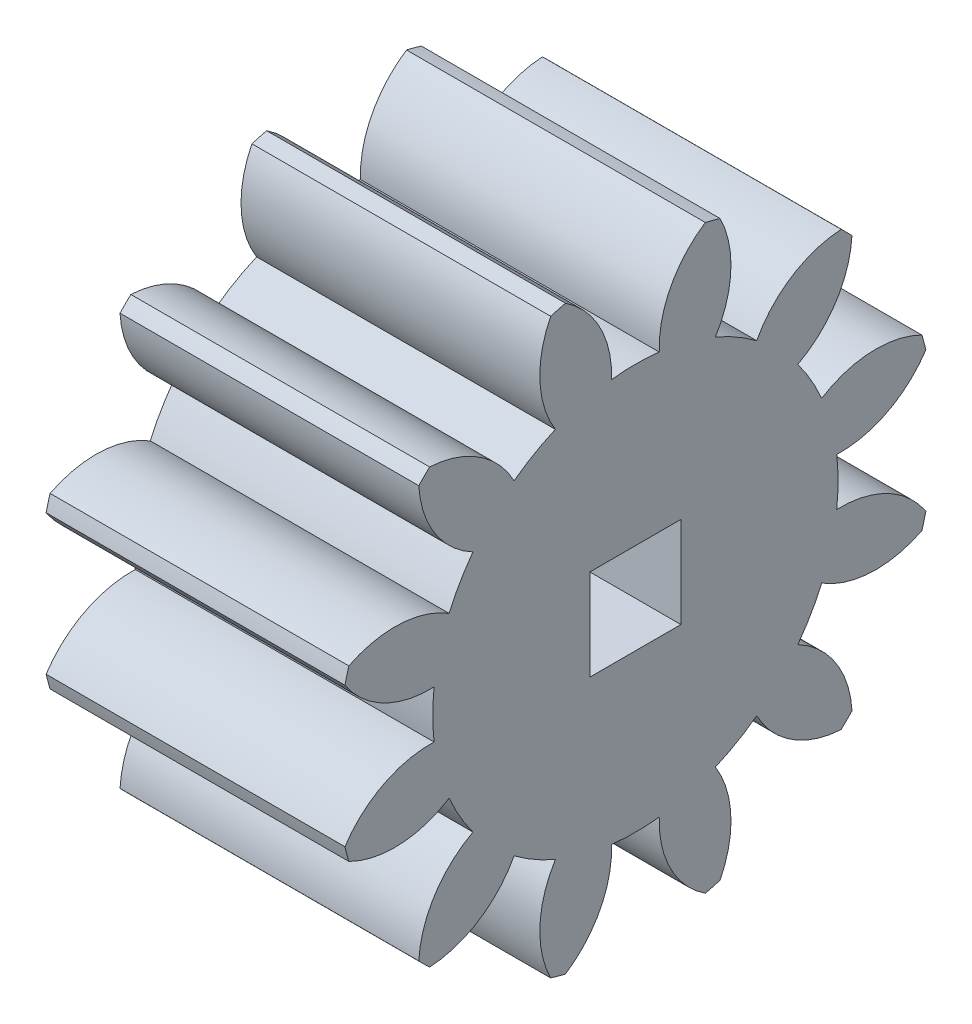
SolidWorks part; units mm, degrees
ref_plane "Plane1" through (0, 0, 0) normal (0, 0, 1) x (1, 0, 0)
ref_plane "Plane2" through (0, 0, 0) normal (0, 1, 0) x (1, 0, 0)
ref_plane "Plane3" through (0, 0, 0) normal (1, 0, 0) x (0, 0, -1)
other "Configuration Table"
sketch "HoldingSke" plane through (0, 0, 0) normal (0, 1, 0) x (1, 0, 0)
  line L0 (0, 0) -> (0.6521, -0.1386)
  line L1 (-15, 0) -> (100, 0) construction
  line L2 (0, 0) -> (-2.1039, 2.3779)
  line L3 (0, 0) -> (-11.863, 4.5341)
  line L4 (0, 0) -> (8.4473, 1.7955)
  line L5 (0, 0) -> (-46.8476, -17.4728)
  line L6 (0, 0) -> (-16.5793, -11.1861)
  line L7 (-2.1039, 2.3779) -> (8.6586, 51.2059)
  line L8 (-76.2, 54.61) -> (-76.1, 54.61)
  line L9 (-71.009, 38.7566) -> (-53.1078, 45.2721)
  line L10 (-76.2, 71.12) -> (104.1128, 71.12)
  line L11 (0, 0) -> (-20, 0)
  line L12 (-76.2, 101.6) -> (-76.147, 101.6)
  line L13 (24.9733, 27.94) -> (52.9518, 28.4284)
  line L14 (24.9733, 27.94) -> (24.9743, 27.94)
  line L15 (24.9733, 27.94) -> (100.4006, 29.5858)
  line L16 (-63.627, -1.5) -> (-12.827, -1.5)
  circle A0 centre (0, 0) radius 0.5
  circle A1 centre (0, 0) radius 7.124
  circle A2 centre (0, 0) radius 37.5
  circle A3 centre (0, 0) radius 0.5
  dimension "MHD" = 14.248
  dimension "Hub_dia" = 75
  dimension "Bore" = 1
  dimension "MBD" = 1
  dimension "Num_teeth" = 12
  dimension "Pitch" = 0.6667
  dimension "Overall_len" = 50
  dimension "Show_teeth" = 12
  dimension "Thickness" = 20
  dimension "OAL" = 50.0001
  dimension "T_dim" = 0.1
  dimension "Ap" = 20
  dimension "H" = 19.05
  dimension "Pitch_radius" = 180.3128
  dimension "Width" = 20
  dimension "Backlash" = 0.053
  dimension "Addendum_fac" = 1
  dimension "Dedendum_fac" = 1.25
  dimension "Clearance_fac" = 0.25
  dimension "Dedendum_add" = 0.001
  dimension "Module" = 1.5
sketch "BasProSke" plane through (0, 0, 0) normal (0, 1, 0) x (1, 0, 0)
  line L0 (-10, 0) -> (60, 0) construction
  line L1 (0, 0) -> (0, 10.5)
  line L2 (0, 0) -> (10.5, 0)
  line L3 (10.5, 0) -> (10.5, 10.5)
  line L4 (10.5, 10.5) -> (0, 10.5)
  dimension "Thickness" = 10.5
  dimension "Diameter" = 21
revolve "Base-Revolve" add sketch "BasProSke" angle 360 about L0
sketch "TooCutSke" plane through (0, 0, 0) normal (1, 0, 0) x (0, 0, -1)
  line L1 (0, 0) -> (0, 107) construction
  line L2 (0, 0) -> (-1.2674, 8.9103) construction
  line L3 (0, 0) -> (-4.625, 17.2606) construction
  line L4 (-1.2674, 8.9103) -> (-2.3125, 8.6303) construction
  arc A0 (0.8378, 7.0746) -> (-0.8378, 7.0746) centre (0, 0) ccw
  arc A1 (2.4865, 10.2275) -> (-2.4865, 10.2275) centre (0, 0) ccw
  circle A2 centre (0, 0) radius 9 construction
  circle A3 centre (0, 0) radius 8.4572 construction
  arc A4 (-0.8378, 7.0746) -> (-2.4865, 10.2275) centre (-4.4355, 7.2007) ccw
  arc A5 (2.4865, 10.2275) -> (0.8378, 7.0746) centre (4.4355, 7.2007) ccw
  dimension "Root_dia" = 14.248
  dimension "Overcut_dia" = 21.0508
  dimension "Pitch_dia" = 18
  dimension "Base_dia" = 16.9145
  dimension "Flank_rad" = 3.6
  dimension "Half_ang" = 15
  dimension "Half_CT" = 1.082
extrude "ToothCut" cut sketch "TooCutSke" along normal through all
fillet "Breaks" [suppressed] radius 0.03
fillet "RootFillets" [suppressed] radius 0.376
pattern_circular "TeethCuts" count 12 every 30 about axis through (-10, 0, 0) along (1, 0, 0) of "ToothCut", "RootFillets", "Breaks"
sketch "HubNeaOneSke" plane through (0, 0, 0) normal (-1, 0, 0) x (0, 0, 1)
  circle A0 centre (0, 0) radius 7.124
  dimension "Diameter" = 14.248
extrude "HubNearOne" [suppressed] add sketch "HubNeaOneSke" along normal blind 39.5001
sketch "HubNeaBotSke" plane through (0, 0, 0) normal (-1, 0, 0) x (0, 0, 1)
  circle A0 centre (0, 0) radius 7.124
  dimension "Diameter" = 14.248
extrude "HubNearBoth" [suppressed] add sketch "HubNeaBotSke" along normal blind 19.75
ref_plane "FarPln" through (10.5, 0, 0) normal (1, 0, 0) x (0, 0, -1)
sketch "HubFarSke" plane through (10.5, 0, 0) normal (1, 0, 0) x (0, 0, -1)
  circle A0 centre (0, 0) radius 7.124
  dimension "Diameter" = 14.248
extrude "HubFar" [suppressed] add sketch "HubFarSke" along normal blind 19.75
sketch "BorSke" plane through (0, 0, 0) normal (1, 0, 0) x (0, 0, -1)
  circle A0 centre (0, 0) radius 0.5
  dimension "Diameter" = 1
extrude "Bore" cut sketch "BorSke" along normal mid plane 100.0001
sketch "KeySke" plane through (0, 0, 0) normal (1, 0, 0) x (0, 0, -1)
  line L0 (-0.05, 0) -> (-0.05, 0.6)
  line L1 (-0.05, 0.6) -> (0.05, 0.6)
  line L2 (0.05, 0.6) -> (0.05, 0)
  line L3 (0, 0) -> (0, 34) construction
  line L4 (-0.05, 0) -> (0.05, 0)
  dimension "Offset" = 0.6
  dimension "Width" = 0.1
extrude "Keyway" [suppressed] cut sketch "KeySke" along normal mid plane 100.0001
pattern_circular "Keyway2" [suppressed] count 2 every 90 about axis through (-10, 0, 0) along (1, 0, 0)
sketch "Sketch1" plane through (10.5, 0, 0) normal (1, 0, 0) x (0, 0, -1)
  line L1 (-1.6, -1.6) -> (1.6, -1.6)
  line L2 (-1.6, -1.6) -> (-1.6, 1.6)
  line L3 (-1.6, 1.6) -> (1.6, 1.6)
  line L4 (1.6, -1.6) -> (1.6, 1.6)
  line L5 (-1.6, -1.6) -> (1.6, 1.6) construction
  line L6 (-1.6, 1.6) -> (1.6, -1.6) construction
  point P0 (0, 0)
  dimension "D1" = 3.2
  dimension "D2" = 3.2
extrude "Cut-Extrude1" cut sketch "Sketch1" against normal blind 30
sketch "Sketch3" plane through (0, 0, 0) normal (0, 1, 0) x (1, 0, 0)
  line L0 (0, 0) -> (10, 0) construction
  line L1 (0, -0.8378) -> (0, 0.8378) construction
  line L2 (10, 0) -> (10, 10) construction
  circle A0 centre (10, 0) radius 3.5
  point P0 (10, 0)
  dimension "D1" = 7
  dimension "D2" = 10
  dimension "D3" = 10
equation "' \"Module@HoldingSke\" = 6.35"
equation "' \"Num_teeth@HoldingSke\" = 12"
equation "' \"Ap@HoldingSke\" =  20"
equation "' \"Ap@HoldingSke\" = 20"
equation "' \"Width@HoldingSke\" = 0.5 * 25.4"
equation "' \"Hub_dia@HoldingSke\"= 1 * 25.4"
equation "' \"Hub_dia@HoldingSke\" = 1 * 25.4"
equation "' \"Overall_len@HoldingSke\" = 1.0 * 25.4"
equation "' \"Bore@HoldingSke\" = 0.75 * 25.4"
equation "' \"T_dim@HoldingSke\" = 0.1 * 25.4"
equation "' \"Width@KeySke\" = 0.25 * 25.4"
equation "' \"Show_teeth@HoldingSke\" = 13"
equation "' \"Backlash@HoldingSke\" = 0.009 * 25.4"
equation "' \"Addendum_fac@HoldingSke\" = 1.0"
equation "' \"Dedendum_fac@HoldingSke\" = 1.25"
equation "' \"Dedendum_add@HoldingSke\" = 0.00005 * 25.4"
equation "' \"Clearance_fac@HoldingSke\" = 0.25"
equation "\"Pitch@HoldingSke\" = 1 / \"Module@HoldingSke\""
equation "\"Overcut_dia@TooCutSke\" = (\"Num_teeth@HoldingSke\" + 2 * \"Addendum_fac@HoldingSke\") / \"Pitch@HoldingSke\" + 0.002 * 25.4"
equation "\"Pitch_dia@TooCutSke\" = \"Num_teeth@HoldingSke\" / \"Pitch@HoldingSke\""
equation "\"Base_dia@TooCutSke\" = \"Num_teeth@HoldingSke\" / \"Pitch@HoldingSke\" * cos((\"Ap@HoldingSke\"  * 3.14159265 / 180))"
equation "\"Root_dia@TooCutSke\" = (\"Num_teeth@HoldingSke\" + 2) / \"Pitch@HoldingSke\" - 2 * (\"Addendum_fac@HoldingSke\" + \"Dedendum_fac@HoldingSke\") / \"Pitch@HoldingSke\" - \"Dedendum_add@HoldingSke\" * 2"
equation "\"Half_ang@TooCutSke\" = 180 / \"Num_teeth@HoldingSke\""
equation "\"Half_CT@TooCutSke\" = \"Num_teeth@HoldingSke\" / \"Pitch@HoldingSke\" * sin((3.14159265 / 2 / \"Num_teeth@HoldingSke\")) / 2 - 7 * \"Backlash@HoldingSke\" / 4"
equation "\"Flank_rad@TooCutSke\" = \"Num_teeth@HoldingSke\" / \"Pitch@HoldingSke\" / 5"
equation "\"Radius@RootFillets\" = \"Clearance_fac@HoldingSke\" / \"Pitch@HoldingSke\" + \"Dedendum_add@HoldingSke\""
equation "\"Break_rad@Breaks\" = 0.02 / \"Pitch@HoldingSke\""
equation "\"Thickness@HoldingSke\" = \"Width@HoldingSke\""
equation "\"OAL@HoldingSke\" = \"Thickness@HoldingSke\""
equation "\"MHD@HoldingSke\" = (\"Num_teeth@HoldingSke\" + 2) / \"Pitch@HoldingSke\" - 2 * (\"Addendum_fac@HoldingSke\" + \"Dedendum_fac@HoldingSke\")  / \"Pitch@HoldingSke\" - \"Dedendum_add@HoldingSke\" * 2"
equation "\"MBD@HoldingSke\" = (\"Num_teeth@HoldingSke\" + 2) / \"Pitch@HoldingSke\" - 2 * (\"Addendum_fac@HoldingSke\" + \"Dedendum_fac@HoldingSke\")  / \"Pitch@HoldingSke\" - \"Dedendum_add@HoldingSke\" * 2 - 0.002 * 25.4"
equation "\"MHD@HoldingSke\" = ((sgn( \"MHD@HoldingSke\" - \"Hub_dia@HoldingSke\" )-1)*( \"MHD@HoldingSke\" - \"Hub_dia@HoldingSke\" ))/-2+ \"Hub_dia@HoldingSke\""
equation "\"MBD@HoldingSke\" = ((sgn( \"MBD@HoldingSke\" - \"Bore@HoldingSke\" )-1)*( \"MBD@HoldingSke\" - \"Bore@HoldingSke\" ))/-2+ \"Bore@HoldingSke\""
equation "\"OAL@HoldingSke\" = ((sgn( \"OAL@HoldingSke\" - \"Overall_len@HoldingSke\" )+1)*( \"OAL@HoldingSke\" - \"Overall_len@HoldingSke\" ))/2 + \"Overall_len@HoldingSke\" + 0.000002 * 25.4"
equation "\"Num_teeth@TeethCuts\" = int( \"Show_teeth@HoldingSke\" ) + 1"
equation "\"Num_teeth@TeethCuts\" = ((sgn( \"Num_teeth@TeethCuts\" - \"Num_teeth@HoldingSke\" )-1)*( \"Num_teeth@TeethCuts\" - \"Num_teeth@HoldingSke\" ))/-2+ \"Num_teeth@HoldingSke\""
equation "\"Num_teeth@TeethCuts\" = ((sgn( \"Num_teeth@TeethCuts\" - 2.0)+1)*( \"Num_teeth@TeethCuts\" - 2.0))/2 +2.0"
equation "\"Angle@TeethCuts\" = 360.0 / \"Num_teeth@HoldingSke\""
equation "\"Diameter@BasProSke\" = (\"Num_teeth@HoldingSke\" + 2 * \"Addendum_fac@HoldingSke\") / \"Pitch@HoldingSke\""
equation "' \"Fillet_rad@BasProSke\" =  \"Thickness@HoldingSke\" * 0.05"
equation "' \"Fillet_rad@BasProSke\" = \"Thickness@HoldingSke\" * 0.05"
equation "\"MHD@HoldingSke\" = ((sgn( \"MHD@HoldingSke\" - \"Root_dia@TooCutSke\" )-1)*( \"MHD@HoldingSke\" - \"Root_dia@TooCutSke\" ))/-2+ \"Root_dia@TooCutSke\""
equation "\"Diameter@HubNeaOneSke\" = \"MHD@HoldingSke\""
equation "\"Length@HubNearOne\" = \"OAL@HoldingSke\" - \"Thickness@BasProSke\""
equation "\"Diameter@HubNeaBotSke\" = \"MHD@HoldingSke\""
equation "\"Length@HubNearBoth\" = ( \"OAL@HoldingSke\" - \"Thickness@BasProSke\" ) / 2.0"
equation "\"Thickness@FarPln\" = \"Thickness@BasProSke\""
equation "\"Diameter@HubFarSke\" = \"MHD@HoldingSke\""
equation "\"Length@HubFar\" = ( \"OAL@HoldingSke\" - \"Thickness@BasProSke\" ) / 2.0"
equation "\"Diameter@BorSke\" = \"MBD@HoldingSke\""
equation "\"D1@Bore\" = \"OAL@HoldingSke\" * 2.0"
equation "\"D1@Keyway\" = \"OAL@HoldingSke\" * 2.0"
equation "\"Offset@KeySke\" = \"T_dim@HoldingSke\" + \"MBD@HoldingSke\" / 2.0"
